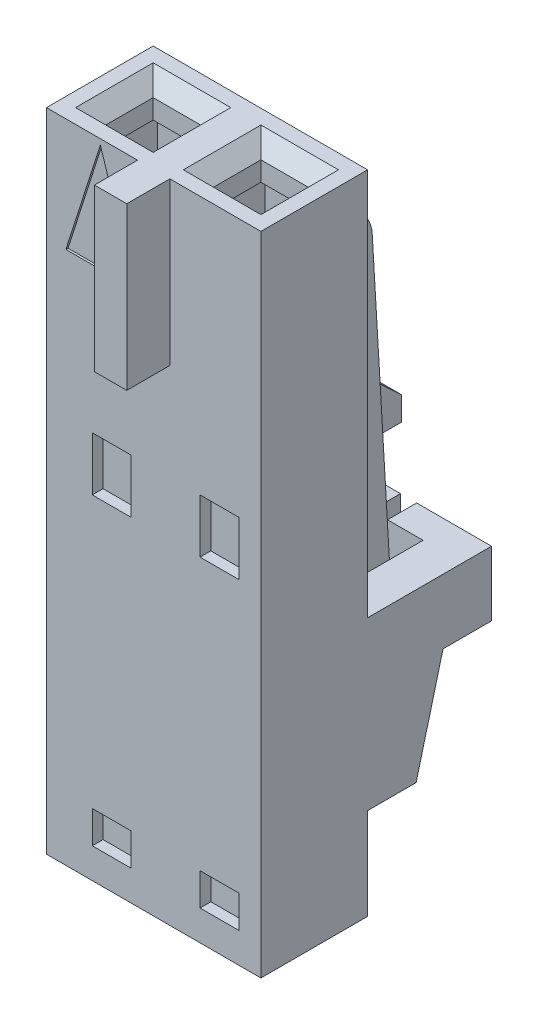
SolidWorks part; units mm, degrees
material "CA"
ref_plane "Front Plane" through (0, 0, 0) normal (0, 0, 1) x (1, 0, 0)
ref_plane "Top Plane" through (0, 0, 0) normal (0, 1, 0) x (1, 0, 0)
ref_plane "Right Plane" through (0, 0, 0) normal (1, 0, 0) x (0, 0, -1)
ref_plane "Plane1" through (0, 0, 1.2573) normal (0, 0, 1) x (1, 0, 0)
sketch "Sketch1" plane through (0, 0, 1.2573) normal (0, 0, 1) x (1, 0, 0)
  line L0 (2.5273, -7.62) -> (2.5273, 7.62)
  line L1 (2.5273, 7.62) -> (-2.5273, 7.62)
  line L2 (-2.5273, 7.62) -> (-2.5273, -7.62)
  line L3 (-2.5273, -7.62) -> (2.5273, -7.62)
extrude "Boss-Extrude1" add sketch "Sketch1" against normal blind 2.5146
ref_plane "Plane2" through (0, 0, 1.2065) normal (0, 0, -1) x (-1, 0, 0)
sketch "Sketch2" plane through (0, 0, 1.2065) normal (0, 0, -1) x (-1, 0, 0)
  line L0 (0.4445, 4.953) -> (2.0701, 4.953)
  line L1 (2.0701, 4.953) -> (1.2573, 7.493)
  line L2 (1.2573, 7.493) -> (0.4445, 4.953)
extrude "Cut-Extrude1" cut sketch "Sketch2" against normal up to next
ref_plane "Plane3" through (-1.2192, 0, 0) normal (-1, 0, 0) x (0, -1, 0)
sketch "Sketch3" plane through (-1.2192, 0, 0) normal (-1, 0, 0) x (0, -1, 0)
  line L0 (5.207, -2.4345) -> (-4.4122, -1.8664)
  line L1 (-4.3942, -1.2573) -> (-5.715, -1.2573)
  line L2 (-5.715, -1.2573) -> (-5.715, -3.0566)
  line L3 (-5.715, -3.0566) -> (3.048, -3.0566)
  line L4 (3.048, -3.0566) -> (3.429, -3.0566)
  line L5 (3.429, -3.0566) -> (3.683, -3.0566)
  line L6 (3.683, -3.0566) -> (4.191, -3.0566)
  line L7 (4.191, -3.0566) -> (4.445, -3.0566)
  line L8 (4.445, -3.0566) -> (4.953, -3.0566)
  line L9 (4.953, -3.0566) -> (5.207, -3.0566)
  line L10 (5.207, -3.0566) -> (5.207, -2.4345)
  arc A0 (-4.4122, -1.8664) -> (-4.3942, -1.2573) centre (-4.3942, -1.5621) cw
extrude "Boss-Extrude2" add sketch "Sketch3" against normal blind 2.4384
chamfer "Chamfer1" distance 3.6894 angle 9.392 1 edges at (0, -5.207, -2.4345)
sketch "Sketch4" plane through (0, 0, -3.0566) normal (0, 0, -1) x (-1, 0, 0)
  line L0 (1.2192, -3.683) -> (1.2192, -4.191)
  line L1 (1.2192, -4.191) -> (1.2192, -4.445)
  line L2 (1.2192, -4.445) -> (1.2192, -4.953)
  line L3 (1.2192, -4.953) -> (1.2192, -5.207)
  line L4 (1.2192, -5.207) -> (0.381, -5.207)
  line L5 (0.381, -5.207) -> (-0.381, -5.207)
  line L6 (-0.381, -5.207) -> (-1.2192, -5.207)
  line L7 (-1.2192, -5.207) -> (-1.2192, -4.953)
  line L8 (-1.2192, -4.953) -> (-1.2192, -4.445)
  line L9 (-1.2192, -4.445) -> (-1.2192, -4.191)
  line L10 (-1.2192, -4.191) -> (-1.2192, -3.683)
  line L11 (-1.2192, -3.683) -> (-1.2192, -3.429)
  line L12 (-1.2192, -3.429) -> (-1.2192, -3.048)
  line L13 (-1.2192, -3.048) -> (-1.2192, -1.524)
  line L14 (-1.2192, -1.524) -> (-0.381, -1.524)
  line L15 (-0.381, -1.524) -> (0.381, -1.524)
  line L16 (0.381, -1.524) -> (1.2192, -1.524)
  line L17 (1.2192, -1.524) -> (1.2192, -3.048)
  line L18 (1.2192, -3.048) -> (1.2192, -3.429)
  line L19 (1.2192, -3.429) -> (1.2192, -3.683)
extrude "Boss-Extrude3" add sketch "Sketch4" along normal blind 1.1217
draft "Draft1" type of draft neutral plane draft angle 3.38 faces to draft 1 face at (0, 2.0955, -3.0566) neutral plane through (1.2192, -1.524, -4.1783) neutral plane normal (0, 1, 0) parameters "D1"=3.38
fillet "Fillet1" radius 0.8128 1 edges at (0, 5.715, -2.6291)
sketch "Sketch5" plane through (-1.2192, 0, 0) normal (-1, 0, 0) x (0, 0, 1)
  line L0 (-4.1783, -1.524) -> (-4.1783, -3.048)
  line L1 (-4.1783, -3.048) -> (-4.1783, -3.429)
  line L2 (-4.1783, -3.429) -> (-4.1783, -3.683)
  line L3 (-4.1783, -3.683) -> (-4.1783, -4.191)
  line L4 (-4.1783, -4.191) -> (-4.1783, -4.445)
  line L5 (-4.1783, -4.445) -> (-4.1783, -4.953)
  line L6 (-4.1783, -4.953) -> (-4.1783, -5.207)
  line L7 (-4.1783, -5.207) -> (-3.0518, -5.207)
  line L8 (-3.0518, -5.207) -> (-2.5624, -3.048)
  line L9 (-2.5624, -3.048) -> (-3.1466, -3.048)
  line L10 (-3.1466, -3.048) -> (-3.0566, -1.524)
  line L11 (-3.0566, -1.524) -> (-4.1783, -1.524)
extrude "Cut-Extrude2" cut sketch "Sketch5" against normal blind 0.8382
sketch "Sketch6" plane through (1.2192, 0, 0) normal (1, 0, 0) x (0, 0, -1)
  line L0 (4.1783, -3.429) -> (4.1783, -3.048)
  line L1 (4.1783, -3.048) -> (4.1783, -1.524)
  line L2 (4.1783, -1.524) -> (3.0566, -1.524)
  line L3 (3.0566, -1.524) -> (3.1466, -3.048)
  line L4 (3.1466, -3.048) -> (2.5624, -3.048)
  line L5 (2.5624, -3.048) -> (3.0518, -5.207)
  line L6 (3.0518, -5.207) -> (4.1783, -5.207)
  line L7 (4.1783, -5.207) -> (4.1783, -4.953)
  line L8 (4.1783, -4.953) -> (4.1783, -4.445)
  line L9 (4.1783, -4.445) -> (4.1783, -4.191)
  line L10 (4.1783, -4.191) -> (4.1783, -3.683)
  line L11 (4.1783, -3.683) -> (4.1783, -3.429)
extrude "Cut-Extrude3" cut sketch "Sketch6" against normal blind 0.8382
ref_plane "Plane4" through (0, 0, -3.5687) normal (0, 0, -1) x (-1, 0, 0)
sketch "Sketch7" plane through (0, 0, -3.5687) normal (0, 0, -1) x (-1, 0, 0)
  line L0 (1.016, 1.1176) -> (-1.016, 1.1176)
  line L1 (-1.016, 1.1176) -> (-1.016, 0.5588)
  line L2 (-1.016, 0.5588) -> (1.016, 0.5588)
  line L3 (1.016, 0.5588) -> (1.016, 1.1176)
extrude "Boss-Extrude4" add sketch "Sketch7" against normal up to surface
draft "Draft2" type of draft neutral plane draft angle 43.044 faces to draft 1 face at (0, 1.1176, -3.2347) neutral plane through (0, 0, -3.5687) neutral plane normal (0, 0, -1) parameters "D1"=43.044
sketch "Sketch8" plane through (0, 0, -1.2573) normal (0, 0, -1) x (-1, 0, 0)
  line L0 (-1.6002, -1.524) -> (-1.6002, -5.461)
  line L1 (-1.6002, -5.461) -> (-2.5273, -5.461)
  line L2 (-2.5273, -5.461) -> (-2.5273, -1.524)
  line L3 (-2.5273, -1.524) -> (-1.6002, -1.524)
extrude "Boss-Extrude5" add sketch "Sketch8" along normal blind 1.778
sketch "Sketch9" plane through (0, 0, -1.2573) normal (0, 0, -1) x (-1, 0, 0)
  line L0 (2.5273, -5.461) -> (1.6002, -5.461)
  line L1 (1.6002, -5.461) -> (1.6002, -1.524)
  line L2 (1.6002, -1.524) -> (2.5273, -1.524)
  line L3 (2.5273, -1.524) -> (2.5273, -5.461)
extrude "Boss-Extrude6" add sketch "Sketch9" along normal blind 1.778
sketch "Sketch10" plane through (0, 0, -3.0353) normal (0, 0, -1) x (-1, 0, 0)
  line L0 (1.6002, -1.524) -> (2.5273, -1.524)
  line L1 (2.5273, -1.524) -> (2.5273, -3.048)
  line L2 (2.5273, -3.048) -> (1.6002, -3.048)
  line L3 (1.6002, -3.048) -> (1.6002, -1.524)
extrude "Boss-Extrude7" add sketch "Sketch10" along normal blind 1.143
sketch "Sketch11" plane through (0, 0, -3.0353) normal (0, 0, -1) x (-1, 0, 0)
  line L0 (-1.6002, -3.048) -> (-2.5273, -3.048)
  line L1 (-2.5273, -3.048) -> (-2.5273, -1.524)
  line L2 (-2.5273, -1.524) -> (-1.6002, -1.524)
  line L3 (-1.6002, -1.524) -> (-1.6002, -3.048)
extrude "Boss-Extrude8" add sketch "Sketch11" along normal blind 1.143
sketch "Sketch12" plane through (1.6002, 0, 0) normal (-1, 0, 0) x (0, 0, 1)
  line L0 (-4.1783, -3.048) -> (-4.1783, -1.524)
  line L1 (-4.1783, -1.524) -> (-3.4925, -1.524)
  line L2 (-3.4925, -1.524) -> (-3.4925, -3.048)
  line L3 (-3.4925, -3.048) -> (-4.1783, -3.048)
extrude "Boss-Extrude9" add sketch "Sketch12" along normal blind 0.8382
sketch "Sketch13" plane through (-1.6002, 0, 0) normal (1, 0, 0) x (0, 0, -1)
  line L0 (3.4925, -1.524) -> (4.1783, -1.524)
  line L1 (4.1783, -1.524) -> (4.1783, -3.048)
  line L2 (4.1783, -3.048) -> (3.4925, -3.048)
  line L3 (3.4925, -3.048) -> (3.4925, -1.524)
extrude "Boss-Extrude10" add sketch "Sketch13" along normal blind 0.8382
draft "Draft3" type of draft neutral plane draft angle 14.744 faces to draft 1 face at (-2.0638, -4.2545, -3.0353) neutral plane through (-2.5273, -3.048, -4.1783) neutral plane normal (0, -1, 0) parameters "D1"=14.744
draft "Draft4" type of draft neutral plane draft angle 14.744 faces to draft 1 face at (2.0638, -4.2545, -3.0353) neutral plane through (1.6002, -3.048, -4.1783) neutral plane normal (0, -1, 0) parameters "D1"=14.744
sketch "Sketch14" plane through (-0.381, 0, 0) normal (-1, 0, 0) x (0, 0, 1)
  line L0 (-4.1783, -3.429) -> (-3.9878, -3.048)
  line L1 (-3.9878, -3.048) -> (-4.1783, -3.048)
  line L2 (-4.1783, -3.048) -> (-4.1783, -3.429)
extrude "Cut-Extrude4" cut sketch "Sketch14" against normal blind 0.762
sketch "Sketch15" plane through (-0.381, 0, 0) normal (-1, 0, 0) x (0, 0, 1)
  line L0 (-4.1783, -4.191) -> (-3.9243, -4.064)
  line L1 (-3.9243, -4.064) -> (-3.9243, -3.81)
  line L2 (-3.9243, -3.81) -> (-4.1783, -3.683)
  line L3 (-4.1783, -3.683) -> (-4.1783, -4.191)
extrude "Cut-Extrude5" cut sketch "Sketch15" against normal blind 0.762
sketch "Sketch16" plane through (-0.381, 0, 0) normal (-1, 0, 0) x (0, 0, 1)
  line L0 (-4.1783, -4.953) -> (-3.9243, -4.826)
  line L1 (-3.9243, -4.826) -> (-3.9243, -4.572)
  line L2 (-3.9243, -4.572) -> (-4.1783, -4.445)
  line L3 (-4.1783, -4.445) -> (-4.1783, -4.953)
extrude "Cut-Extrude6" cut sketch "Sketch16" against normal blind 0.762
sketch "Sketch17" plane through (0, 0, 1.2573) normal (0, 0, 1) x (1, 0, 0)
  line L0 (-0.381, 3.81) -> (-0.381, 7.62)
  line L1 (-0.381, 7.62) -> (0.381, 7.62)
  line L2 (0.381, 7.62) -> (0.381, 3.81)
  line L3 (0.381, 3.81) -> (-0.381, 3.81)
extrude "Boss-Extrude11" add sketch "Sketch17" along normal blind 1.016
sketch "Sketch18" plane through (0, 0, 1.2573) normal (0, 0, 1) x (1, 0, 0)
  line L0 (2.0066, 0.254) -> (2.0066, 1.524)
  line L1 (2.0066, 1.524) -> (1.0922, 1.524)
  line L2 (1.0922, 1.524) -> (1.0922, 0.254)
  line L3 (1.0922, 0.254) -> (2.0066, 0.254)
extrude "Cut-Extrude7" cut sketch "Sketch18" against normal blind 0.254
sketch "Sketch19" plane through (0, 0, 1.2573) normal (0, 0, 1) x (1, 0, 0)
  line L0 (2.0066, -6.9088) -> (2.0066, -6.1468)
  line L1 (2.0066, -6.1468) -> (1.0922, -6.1468)
  line L2 (1.0922, -6.1468) -> (1.0922, -6.9088)
  line L3 (1.0922, -6.9088) -> (2.0066, -6.9088)
extrude "Cut-Extrude8" cut sketch "Sketch19" against normal blind 0.254
sketch "Sketch20" plane through (0, 0, 1.2573) normal (0, 0, 1) x (1, 0, 0)
  line L0 (-0.5334, 0.254) -> (-0.5334, 1.524)
  line L1 (-0.5334, 1.524) -> (-1.4478, 1.524)
  line L2 (-1.4478, 1.524) -> (-1.4478, 0.254)
  line L3 (-1.4478, 0.254) -> (-0.5334, 0.254)
extrude "Cut-Extrude9" cut sketch "Sketch20" against normal blind 0.254
sketch "Sketch21" plane through (0, 0, 1.2573) normal (0, 0, 1) x (1, 0, 0)
  line L0 (-0.5334, -6.9088) -> (-0.5334, -6.1468)
  line L1 (-0.5334, -6.1468) -> (-1.4478, -6.1468)
  line L2 (-1.4478, -6.1468) -> (-1.4478, -6.9088)
  line L3 (-1.4478, -6.9088) -> (-0.5334, -6.9088)
extrude "Cut-Extrude10" cut sketch "Sketch21" against normal blind 0.254
sketch "Sketch22" plane through (0, -7.62, 0) normal (0, -1, 0) x (1, 0, 0)
  line L0 (-0.3429, 0.889) -> (-2.1971, 0.889)
  line L1 (-2.1971, 0.889) -> (-2.1971, -0.889)
  line L2 (-2.1971, -0.889) -> (-0.3429, -0.889)
  line L3 (-0.3429, -0.889) -> (-0.3429, 0.889)
extrude "Cut-Extrude11" cut sketch "Sketch22" against normal blind 8.636
sketch "Sketch23" plane through (0, -7.62, 0) normal (0, -1, 0) x (1, 0, 0)
  line L0 (0.3429, 0.889) -> (0.3429, -0.889)
  line L1 (0.3429, -0.889) -> (2.1971, -0.889)
  line L2 (2.1971, -0.889) -> (2.1971, 0.889)
  line L3 (2.1971, 0.889) -> (0.3429, 0.889)
extrude "Cut-Extrude12" cut sketch "Sketch23" against normal blind 8.636
chamfer "Chamfer2" distance 0.0762 angle 73.301 4 edges at (-1.27, 1.016, -0.889) (-0.3429, 1.016, 0) (-2.1971, 1.016, 0) (-1.27, 1.016, 0.889)
chamfer "Chamfer3" distance 0.2159 angle 49.635 4 edges at (2.1971, 1.016, 0) (1.27, 1.016, 0.889) (1.27, 1.016, -0.889) (0.3429, 1.016, 0)
sketch "Sketch24" plane through (0, -7.62, 0) normal (0, -1, 0) x (1, 0, 0)
  line L0 (-0.6477, -1.2573) -> (-0.6477, -0.889)
  line L1 (-0.6477, -0.889) -> (-1.9177, -0.889)
  line L2 (-1.9177, -0.889) -> (-1.9177, -1.2573)
  line L3 (-1.9177, -1.2573) -> (-0.6477, -1.2573)
extrude "Cut-Extrude13" cut sketch "Sketch24" against normal blind 1.016
sketch "Sketch25" plane through (0, -7.62, 0) normal (0, -1, 0) x (1, 0, 0)
  line L0 (1.8923, -1.2573) -> (1.8923, -0.889)
  line L1 (1.8923, -0.889) -> (0.6223, -0.889)
  line L2 (0.6223, -0.889) -> (0.6223, -1.2573)
  line L3 (0.6223, -1.2573) -> (1.8923, -1.2573)
extrude "Cut-Extrude14" cut sketch "Sketch25" against normal blind 1.016
sketch "Sketch26" plane through (0, 1.016, 0) normal (0, -1, 0) x (1, 0, 0)
  line L0 (-1.9812, -0.8128) -> (-0.5588, -0.8128)
  line L1 (-0.5588, -0.8128) -> (-0.5588, 0.8128)
  line L2 (-0.5588, 0.8128) -> (-1.9812, 0.8128)
  line L3 (-1.9812, 0.8128) -> (-1.9812, -0.8128)
extrude "Cut-Extrude15" cut sketch "Sketch26" against normal blind 5.7912
sketch "Sketch27" plane through (0, 1.016, 0) normal (0, -1, 0) x (1, 0, 0)
  line L0 (0.5588, -0.8128) -> (1.9812, -0.8128)
  line L1 (1.9812, -0.8128) -> (1.9812, 0.8128)
  line L2 (1.9812, 0.8128) -> (0.5588, 0.8128)
  line L3 (0.5588, 0.8128) -> (0.5588, -0.8128)
extrude "Cut-Extrude16" cut sketch "Sketch27" against normal blind 5.7912
sketch "Sketch28" plane through (0, 6.8072, 0) normal (0, -1, 0) x (1, 0, 0)
  line L0 (1.8288, -0.5588) -> (1.8288, 0.5588)
  line L1 (1.8288, 0.5588) -> (0.7112, 0.5588)
  line L2 (0.7112, 0.5588) -> (0.7112, -0.5588)
  line L3 (0.7112, -0.5588) -> (1.8288, -0.5588)
extrude "Cut-Extrude17" cut sketch "Sketch28" against normal through all
sketch "Sketch29" plane through (0, 6.8072, 0) normal (0, -1, 0) x (1, 0, 0)
  line L0 (-0.7112, 0.5588) -> (-1.8288, 0.5588)
  line L1 (-1.8288, 0.5588) -> (-1.8288, -0.5588)
  line L2 (-1.8288, -0.5588) -> (-0.7112, -0.5588)
  line L3 (-0.7112, -0.5588) -> (-0.7112, 0.5588)
extrude "Cut-Extrude18" cut sketch "Sketch29" against normal through all
chamfer "Chamfer4" distance 0.3556 angle 45 4 edges at (1.27, 7.62, -0.5588) (0.7112, 7.62, 0) (1.8288, 7.62, 0) (1.27, 7.62, 0.5588)
chamfer "Chamfer5" distance 0.3556 angle 45 4 edges at (-0.7112, 7.62, 0) (-1.27, 7.62, -0.5588) (-1.27, 7.62, 0.5588) (-1.8288, 7.62, 0)
